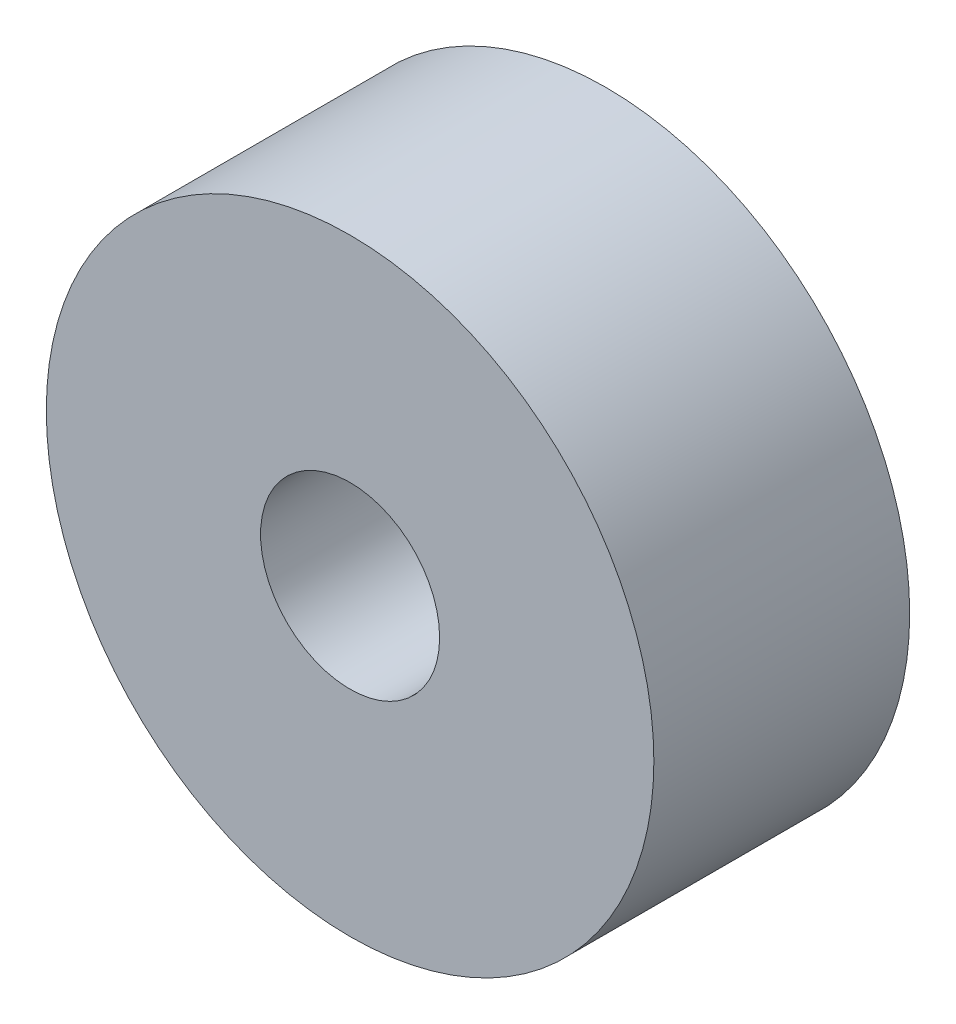
SolidWorks part; units mm, degrees
ref_plane "Front Plane" through (0, 0, 0) normal (0, 0, 1) x (1, 0, 0)
ref_plane "Top Plane" through (0, 0, 0) normal (0, 1, 0) x (1, 0, 0)
ref_plane "Right Plane" through (0, 0, 0) normal (1, 0, 0) x (0, 0, -1)
sketch "Sketch1" plane through (0, 0, 0) normal (0, 0, 1) x (1, 0, 0)
  circle A0 centre (0, 0) radius 9.5
  dimension "D1" = 19
extrude "Main Extrude" add sketch "Sketch1" along normal blind 8
sketch "Sketch2" plane through (0, 0, 8) normal (0, 0, 1) x (1, 0, 0)
  circle A0 centre (0, 0) radius 2.8
  dimension "D1" = 5.6
ref_plane "Halfway front plane" through (0, 0, 3) normal (0, 0, 1) x (1, 0, 0)
extrude "Cut-Extrude1" cut sketch "Sketch2" against normal blind 10
